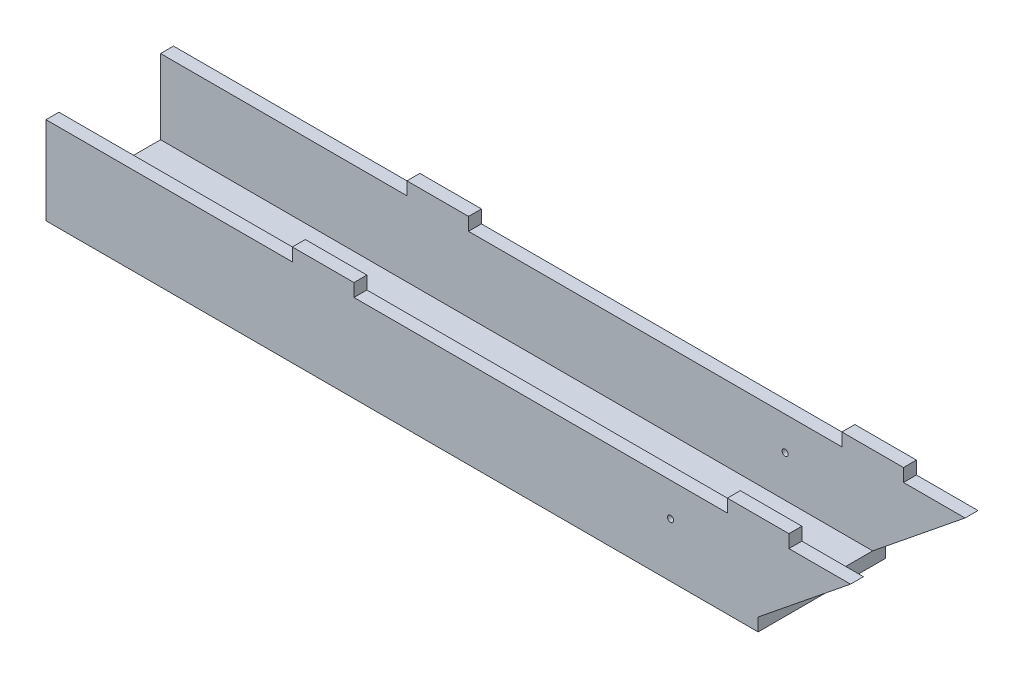
SolidWorks part; units mm, degrees
material "Polyurethane Foam Rigid"
ref_plane "Front" through (0, 0, 0) normal (0, 0, 1) x (1, 0, 0)
ref_plane "Top" through (0, 0, 0) normal (0, 1, 0) x (1, 0, 0)
ref_plane "Right" through (0, 0, 0) normal (1, 0, 0) x (0, 0, -1)
sketch "Sketch2" plane through (0, 0, 0) normal (0, 1, 0) x (1, 0, 0)
  line L1 (-146.8438, -26.289) -> (146.8438, -26.289)
  line L2 (-146.8438, -26.289) -> (-146.8438, 26.289)
  line L3 (-146.8438, 26.289) -> (146.8438, 26.289)
  line L4 (146.8438, -26.289) -> (146.8438, 26.289)
  line L5 (-146.8438, -26.289) -> (146.8438, 26.289) construction
  line L6 (-146.8438, 26.289) -> (146.8438, -26.289) construction
  point P0 (0, 0)
  dimension "D1" = 293.6875
  dimension "D2" = 52.578
extrude "Boss-Extrude1" add sketch "Sketch2" along normal blind 5.334
sketch "Sketch3" plane through (0, 0, 26.289) normal (0, 0, 1) x (1, 0, 0)
  line L0 (-146.8438, 0) -> (146.8438, 0) construction
  line L1 (-146.8438, 5.334) -> (146.8438, 5.334)
  line L2 (-146.8438, 5.334) -> (-146.8438, 36.1188)
  line L3 (-146.8438, 36.1188) -> (146.8438, 36.1188)
  line L4 (146.8438, 5.334) -> (146.8438, 0) construction
  line L6 (146.8438, 36.1188) -> (184.9437, 36.1188)
  line L7 (184.9437, 36.1188) -> (146.8438, 5.334)
  line L9 (159.5437, 36.1188) -> (134.1437, 36.1188)
  line L10 (159.5437, 36.1188) -> (159.5437, 41.4528)
  line L11 (159.5437, 41.4528) -> (134.1437, 41.4528)
  line L12 (134.1437, 36.1188) -> (134.1437, 41.4528)
  line L13 (-45.2437, 36.1188) -> (-19.8438, 36.1188)
  line L14 (-45.2437, 36.1188) -> (-45.2437, 41.4528)
  line L15 (-45.2437, 41.4528) -> (-19.8438, 41.4528)
  line L16 (-19.8438, 36.1188) -> (-19.8438, 41.4528)
  point P12 (146.8438, 2.667)
  line M14 (146.8438, 5.334) -> (-146.8438, 5.334)
  dimension "D1" = 36.1188
  dimension "D2" = 38.1
  dimension "D3" = 25.4
  dimension "D4" = 25.4
  dimension "D5" = 5.334
  dimension "D6" = 25.4
  dimension "D7" = 5.334
  dimension "D8" = 101.6
extrude "Boss-Extrude2" add sketch "Sketch3" against normal blind 5.334 contours L7 L6 L3 L2 M14 | L3 L16 L15 L14 | L12 L3 L6 L10 L11
mirror "Mirror1" about plane through (0, 0, 0) normal (0, 0, 1) of "Boss-Extrude2"
sketch "Sketch4" plane through (0, 0, 26.289) normal (0, 0, 1) x (1, 0, 0)
  line L0 (377.9637, -6.6802) -> (377.9637, 347.9865) construction
  circle A0 centre (110.7447, 22.3424) radius 1.27
  dimension "D1" = 2.54
extrude "BBQ Skewer Holes" cut sketch "Sketch4" against normal through all
sketch "Build Plan" [suppressed] plane through (0, 0, 0) normal (0, -1, 0) x (1, 0, 0)
  line L0 (0, 0) -> (146.8438, 0) construction
  line L1 (-146.8438, 31.623) -> (146.8438, 31.623)
  line L2 (-146.8438, 31.623) -> (-146.8438, 62.4078)
  line L3 (-146.8438, 62.4078) -> (-45.2437, 62.4078)
  line L4 (146.8438, -26.289) -> (146.8438, 26.289)
  line L5 (146.8438, 26.289) -> (-146.8438, 26.289)
  line L6 (-146.8438, 26.289) -> (-146.8438, -26.289)
  line L7 (-146.8438, -26.289) -> (146.8438, -26.289)
  line L8 (146.8438, -26.289) -> (146.8438, 26.289)
  line L9 (146.8438, 26.289) -> (-146.8438, 26.289)
  line L10 (-146.8438, 26.289) -> (-146.8438, -26.289)
  line L11 (-146.8438, -26.289) -> (146.8438, -26.289)
  line L12 (159.5438, 62.4078) -> (184.9438, 62.4078)
  line L13 (184.9438, 62.4078) -> (146.8438, 31.623)
  line L14 (-19.8437, 62.4078) -> (134.1438, 62.4078)
  line L15 (159.5438, 62.4078) -> (159.5438, 68.7578)
  line L16 (159.5438, 68.7578) -> (134.1438, 68.7578)
  line L17 (134.1438, 62.4078) -> (134.1438, 68.7578)
  line L18 (-45.2437, 62.4078) -> (-45.2437, 68.7578)
  line L19 (-45.2437, 68.7578) -> (-19.8437, 68.7578)
  line L20 (-19.8437, 62.4078) -> (-19.8437, 68.7578)
  line L21 (-146.8438, -31.623) -> (146.8438, -31.623)
  line L22 (-146.8438, -31.623) -> (-146.8438, -62.4078)
  line L23 (-146.8438, -62.4078) -> (-45.2437, -62.4078)
  line L24 (159.5438, -62.4078) -> (184.9438, -62.4078)
  line L25 (184.9438, -62.4078) -> (146.8438, -31.623)
  line L26 (-19.8437, -62.4078) -> (134.1438, -62.4078)
  line L27 (159.5438, -62.4078) -> (159.5438, -68.7578)
  line L28 (159.5438, -68.7578) -> (134.1438, -68.7578)
  line L29 (134.1438, -62.4078) -> (134.1438, -68.7578)
  line L30 (-45.2437, -62.4078) -> (-45.2437, -68.7578)
  line L31 (-45.2437, -68.7578) -> (-19.8437, -68.7578)
  line L32 (-19.8437, -62.4078) -> (-19.8437, -68.7578)
  dimension "D1" = 0
